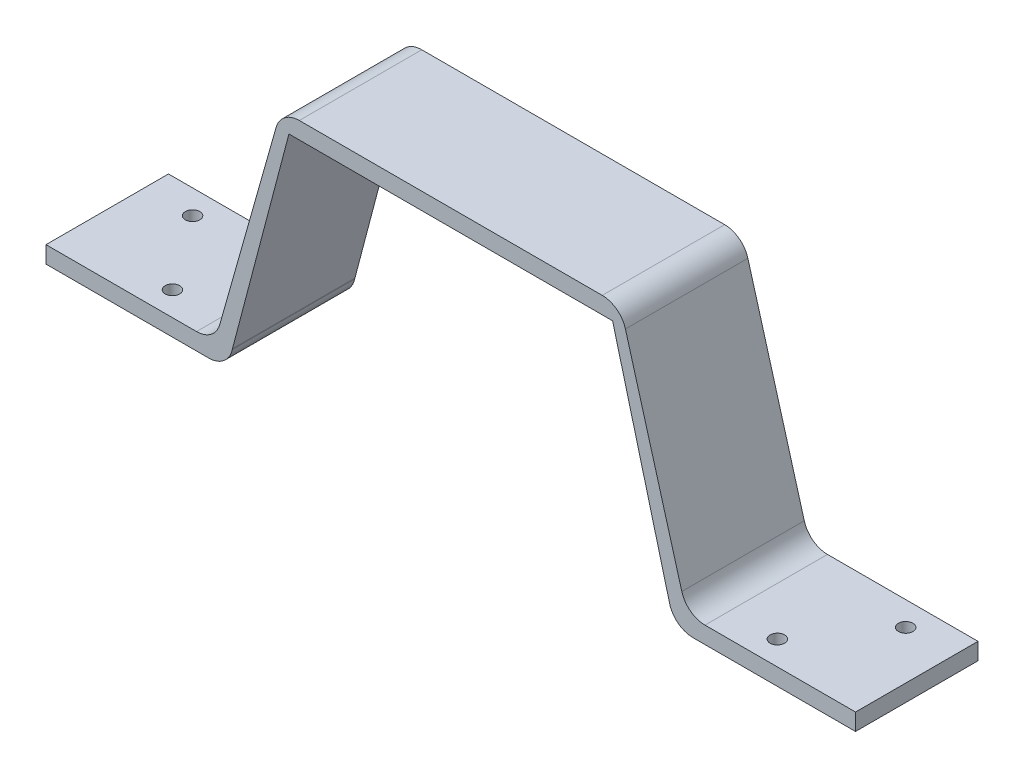
SolidWorks part; units mm, degrees
ref_plane "Alzado" through (0, 0, 0) normal (0, 0, 1) x (1, 0, 0)
ref_plane "Planta" through (0, 0, 0) normal (0, 1, 0) x (1, 0, 0)
ref_plane "Vista lateral" through (0, 0, 0) normal (1, 0, 0) x (0, 0, -1)
sketch "Croquis1" plane through (0, 0, 0) normal (0, 0, 1) x (1, 0, 0)
  line L1 (0, 0) -> (-167.894, 0)
  line L2 (0, 0) -> (0, 52.07)
  line L3 (0, 52.07) -> (-167.894, 52.07)
  line L4 (-167.894, 0) -> (-167.894, 52.07)
  dimension "D1" = 52.07
  dimension "D2" = 167.894
extrude "Saliente-Extruir1" add sketch "Croquis1" along normal blind 25.4
sketch "Croquis2" plane through (0, 0, 25.4) normal (0, 0, 1) x (1, 0, 0)
  line L0 (-167.894, 0) -> (0, 0) construction
  line L1 (-167.894, 52.07) -> (-132.894, 52.07)
  line L2 (-167.894, 52.07) -> (-167.894, 3.5)
  line L3 (-167.894, 3.5) -> (-132.894, 3.5)
  line L4 (-132.894, 52.07) -> (-132.894, 3.5)
  line L5 (-83.947, 52.07) -> (-83.947, 0) construction
  line L6 (0, 52.07) -> (-167.894, 52.07) construction
  line L7 (0, 3.5) -> (-35, 3.5)
  line L8 (-35, 52.07) -> (-35, 3.5)
  line L9 (0, 52.07) -> (-35, 52.07)
  line L10 (0, 52.07) -> (0, 3.5)
  line L11 (-132.894, 3.5) -> (-119.138, 52.07)
  line L12 (-119.138, 52.07) -> (-132.894, 52.07)
  line L13 (-35, 3.5) -> (-48.756, 52.07)
  line L14 (-48.756, 52.07) -> (-35, 52.07)
  line L15 (-120.1292, 48.57) -> (-47.7648, 48.57)
  line L16 (-129.394, 3.5) -> (-115.1292, 48.57)
  line L17 (-129.394, 3.5) -> (-129.394, 0)
  line L18 (-38.5, 3.5) -> (-38.5, 0)
  line L19 (-35, 3.5) -> (-48.756, 52.07)
  line L20 (-38.5, 3.5) -> (-52.7648, 48.57)
  point P19 (-129.394, 3.5)
  line M9 (0, 0) -> (0, 52.07)
  line M10 (0, 52.07) -> (-167.894, 52.07)
  line M11 (-167.894, 52.07) -> (-167.894, 0)
  dimension "D1" = 3.5
  dimension "D2" = 35
  dimension "D3" = 3.5
  dimension "D4" = 3.5
  dimension "D5" = 5
extrude "Cortar-Extruir1" cut sketch "Croquis2" against normal blind 25.4 contours L4 L11 M10 | L4 L3 M10 M11 | L8 L7 M10 M9 | L13 L8 M10
sketch "Croquis3" plane through (0, 0, 25.4) normal (0, 0, 1) x (1, 0, 0)
  line L0 (-117.5091, 48.57) -> (-50.3849, 48.57)
  line L1 (-50.3849, 48.57) -> (-38.5, 3.5)
  line L2 (-38.5, 3.5) -> (-38.5, 0)
  line L3 (-48.756, 52.07) -> (-119.138, 52.07) construction
  line L4 (-83.947, 48.57) -> (-83.947, 0) construction
  line L5 (-167.894, 0) -> (0, 0) construction
  line L7 (-129.394, 3.5) -> (-129.394, 0)
  line L8 (-117.5091, 48.57) -> (-129.394, 3.5)
  line L9 (-38.5, 0) -> (-129.394, 0)
  line L10 (-117.5091, 48.57) -> (-50.3849, 48.57)
  point P6 (-35, 3.5)
  line M8 (-167.894, 0) -> (0, 0)
  dimension "D1" = 3.5
  dimension "D2" = 3.5
  dimension "D3" = 3.5
  dimension "D4" = 3.5
extrude "Cortar-Extruir2" cut sketch "Croquis3" against normal blind 25.4 contours L4 L0 L8 L7 M8 | L10 L4 L9 L2 L1
fillet "Redondeo1" radius 5 1 edges at (-48.756, 52.07, 12.7)
fillet "Redondeo2" radius 5 1 edges at (-119.138, 52.07, 12.7)
fillet "Redondeo6" radius 5 1 edges at (-38.5, 3.5, 12.7)
fillet "Redondeo7" radius 5 1 edges at (-129.394, 3.5, 12.7)
fillet "Redondeo11" radius 5 1 edges at (-129.394, 0, 12.7)
fillet "Redondeo12" radius 5 1 edges at (-38.5, 0, 12.7)
fillet "Redondeo13" radius 5 2 edges at (-132.894, 3.5, 12.7) (-35, 3.5, 12.7)
sketch "Croquis4" plane through (0, 52.07, 0) normal (0, 1, 0) x (1, 0, 0)
  line L0 (-167.894, 0) -> (-167.894, -25.4) construction
  line L1 (-167.894, 0) -> (-136.6746, 0) construction
  line L2 (-136.6746, -25.4) -> (-136.6746, 0) construction
  line L3 (-167.894, -25.4) -> (-136.6746, -25.4) construction
  line L4 (-83.947, 0) -> (-83.947, -25.4) construction
  line L5 (-52.5366, 0) -> (-115.3574, 0) construction
  line L6 (-52.5366, -25.4) -> (-115.3574, -25.4) construction
  circle A0 centre (-157.894, -5) radius 1.5
  circle A1 centre (-146.6746, -20.4) radius 1.5
  circle A2 centre (-21.2194, -20.4) radius 1.5
  circle A3 centre (-10, -5) radius 1.5
  dimension "D5" = 3
  dimension "D1" = 10
  dimension "D2" = 5
  dimension "D3" = 10
  dimension "D4" = 5
extrude "Cortar-Extruir3" cut sketch "Croquis4" against normal blind 76.2
